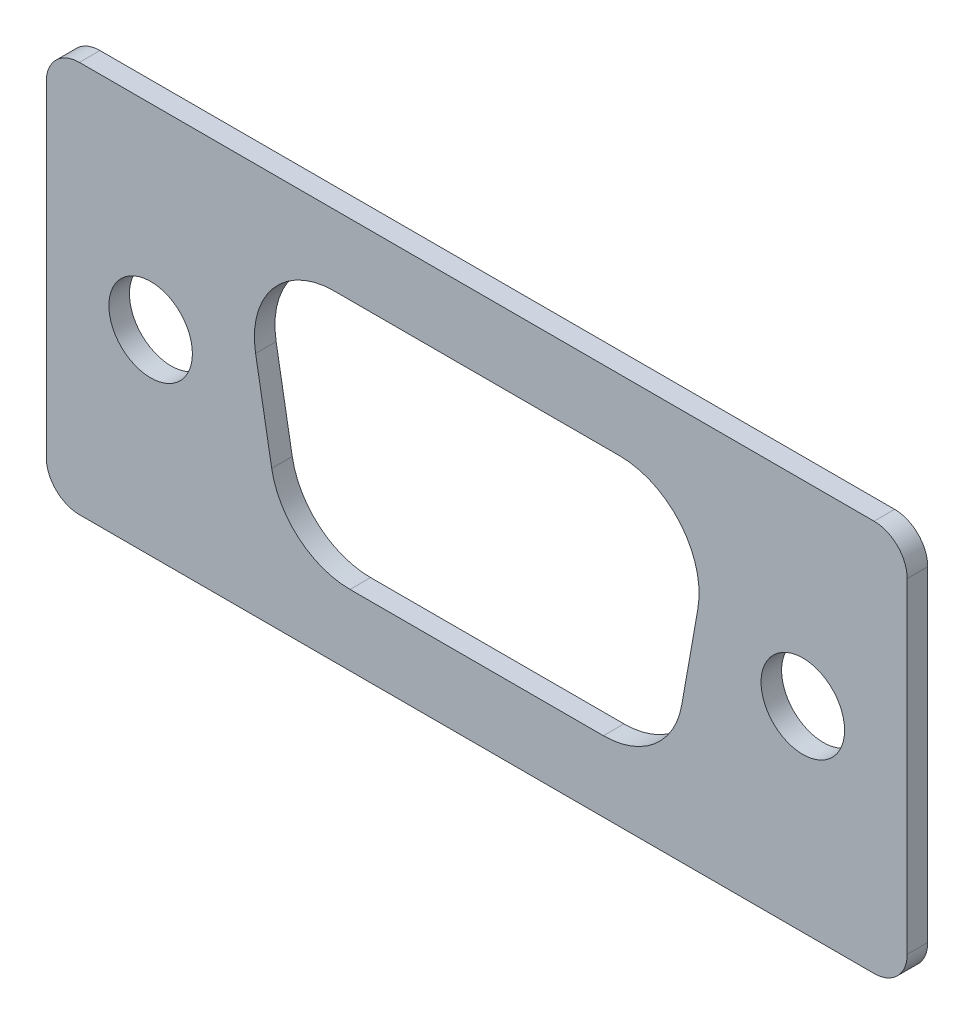
SolidWorks part; units mm, degrees
material "Silicon"
ref_plane "Front Plane" through (0, 0, 0) normal (0, 0, 1) x (1, 0, 0)
ref_plane "Top Plane" through (0, 0, 0) normal (0, 1, 0) x (1, 0, 0)
ref_plane "Right Plane" through (0, 0, 0) normal (1, 0, 0) x (0, 0, -1)
sketch "Sketch1" plane through (0, 0, 0) normal (0, 0, 1) x (1, 0, 0)
  line L0 (16.495, 15.01) -> (16.495, 0) construction
  line L1 (1.27, 0) -> (31.72, 0)
  line L2 (0, 1.27) -> (0, 13.74)
  line L3 (1.27, 15.01) -> (31.72, 15.01)
  line L4 (32.99, 1.27) -> (32.99, 13.74)
  line L5 (0, 7.505) -> (32.99, 7.505) construction
  line L6 (11.0225, 12.305) -> (21.9675, 12.305)
  line L7 (24.9692, 8.7277) -> (24.3514, 5.2237)
  line L8 (21.3497, 2.705) -> (11.6403, 2.705)
  line L9 (8.6386, 5.2237) -> (8.0208, 8.7277)
  line L10 (7.39, 12.305) -> (7.39, 2.705) construction
  line L11 (7.39, 2.705) -> (9.0827, 2.705) construction
  line L12 (25.6, 12.305) -> (25.6, 2.705) construction
  line L13 (25.6, 2.705) -> (23.9073, 2.705) construction
  circle A0 centre (4, 7.505) radius 1.6002
  circle A1 centre (28.99, 7.505) radius 1.6002
  arc A2 (11.6403, 2.705) -> (8.6386, 5.2237) centre (11.6403, 5.753) cw
  arc A3 (24.3514, 5.2237) -> (21.3497, 2.705) centre (21.3497, 5.753) cw
  arc A4 (21.9675, 12.305) -> (24.9692, 8.7277) centre (21.9675, 9.257) cw
  arc A5 (11.0225, 12.305) -> (8.0208, 8.7277) centre (11.0225, 9.257) ccw
  arc A6 (31.72, 15.01) -> (32.99, 13.74) centre (31.72, 13.74) cw
  arc A7 (31.72, 0) -> (32.99, 1.27) centre (31.72, 1.27) ccw
  arc A8 (1.27, 0) -> (0, 1.27) centre (1.27, 1.27) cw
  arc A9 (0, 13.74) -> (1.27, 15.01) centre (1.27, 13.74) cw
  point P37 (0, 0)
  dimension "D3" = 3.2004
  dimension "D6" = 3.048
  dimension "D8" = 18.21
  dimension "D9" = 1.27
  dimension "D1" = 15.01
  dimension "D2" = 32.99
  dimension "D4" = 24.99
  dimension "D5" = 10
  dimension "D7" = 9.6
extrude "Boss-Extrude1" add sketch "Sketch1" along normal blind 0.7874
